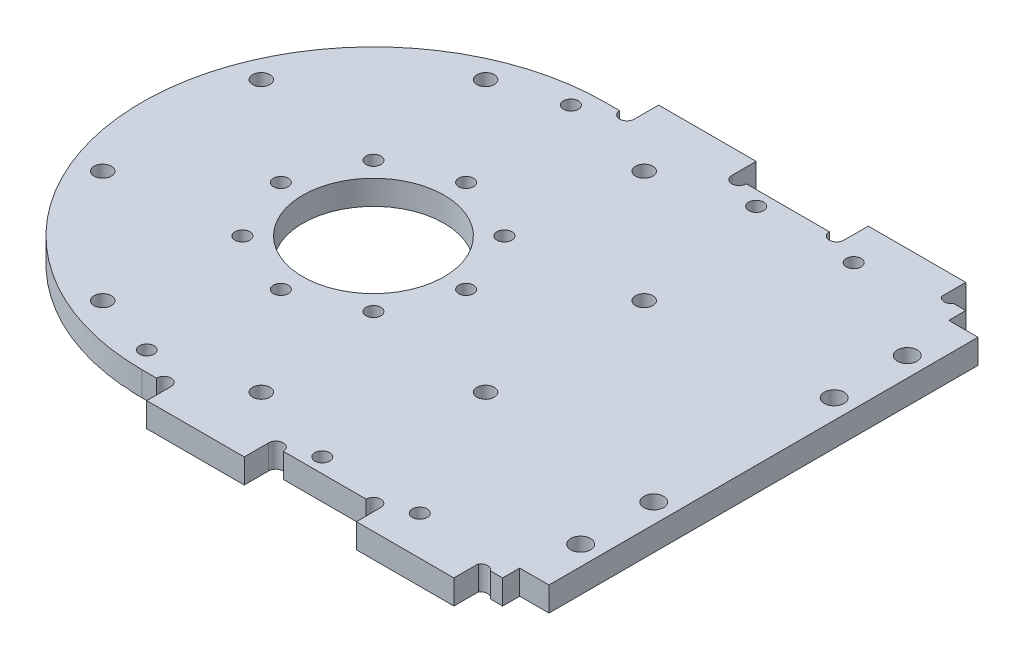
SolidWorks part; units mm, degrees
material "Thornel Mat VMA"
ref_plane "前视基准面" through (0, 0, 0) normal (0, 0, 1) x (1, 0, 0)
ref_plane "上视基准面" through (0, 0, 0) normal (0, 1, 0) x (1, 0, 0)
ref_plane "右视基准面" through (0, 0, 0) normal (1, 0, 0) x (0, 0, -1)
other "Configuration Table"
sketch "草图1" plane through (0, 0, 0) normal (0, 1, 0) x (1, 0, 0)
  line L0 (0, 47.5) -> (80, 47.5)
  line L1 (80, 47.5) -> (80, -47.5)
  line L2 (80, -47.5) -> (0, -47.5)
  arc A0 (0, 47.5) -> (0, -47.5) centre (0, 0) ccw
  dimension "D1" = 47.5
  dimension "D2" = 80
extrude "凸台-拉伸1" add sketch "草图1" along normal mid plane 5
fillet "圆角1" radius 3 2 edges at (80, 0, -47.5) (80, 0, 47.5)
sketch "草图2" plane through (0, 2.5, 0) normal (0, 1, 0) x (1, 0, 0)
  line L0 (-39.2649, 16.264) -> (0, 0) construction
  line L1 (0, 0) -> (-42.5, 0) construction
  circle A0 centre (0, 0) radius 42.5 construction
  circle A1 centre (-39.2649, 16.264) radius 1.775
  circle A2 centre (-16.264, 39.2649) radius 1.775
  circle A3 centre (16.264, 39.2649) radius 1.775
  circle A4 centre (39.2649, 16.264) radius 1.775
  circle A5 centre (39.2649, -16.264) radius 1.775
  circle A6 centre (16.264, -39.2649) radius 1.775
  circle A7 centre (-16.264, -39.2649) radius 1.775
  circle A8 centre (-39.2649, -16.264) radius 1.775
  point P22 (0, 0)
  dimension "D2" = 3.55
  dimension "D3" = 85
  dimension "D1" = 22.5
  dimension "D4" = 8
extrude "切除-拉伸1" cut sketch "草图2" against normal through all both and the other way through all
sketch "草图3" plane through (0, 2.5, 0) normal (0, 1, 0) x (1, 0, 0)
  line L0 (16, 6) -> (16, -6.5) construction
  line L1 (18, -8.5) -> (24.1402, -8.5) construction
  line L2 (24.2693, 8) -> (18, 8) construction
  line L3 (-3.5, -22.1) -> (3.5, -22.1) construction
  line L4 (5.9, -24.5) -> (5.9, -29.7951) construction
  line L5 (-5.9, -29.7951) -> (-5.9, -24.5) construction
  line L6 (-20.8746, 17.5) -> (-16.5, 17.5) construction
  line L7 (-14.5, 15.5) -> (-14.5, -15.5) construction
  line L8 (-16.5, -17.5) -> (-20.8746, -17.5) construction
  line L9 (16, 6) -> (16, -6.5)
  line L10 (18, -8.5) -> (24.1402, -8.5)
  line L11 (24.2693, 8) -> (18, 8)
  line L12 (-3.5, -22.1) -> (3.5, -22.1)
  line L13 (5.9, -24.5) -> (5.9, -29.7951)
  line L14 (-5.9, -29.7951) -> (-5.9, -24.5)
  line L15 (-20.8746, 17.5) -> (-16.5, 17.5)
  line L16 (-14.5, 15.5) -> (-14.5, -15.5)
  line L17 (-16.5, -17.5) -> (-20.8746, -17.5)
  line L18 (-20.8746, 20) -> (-16.5, 20)
  line L19 (-12, 15.5) -> (-12, -15.5)
  line L20 (-16.5, -20) -> (-20.8746, -20)
  line L21 (15, 6) -> (15, -6.5)
  line L22 (18, -9.5) -> (24.1402, -9.5)
  line L23 (24.2693, 9) -> (18, 9)
  line L24 (-3.5, -21.1) -> (3.5, -21.1)
  line L25 (6.9, -24.5) -> (6.9, -29.7951)
  line L26 (-6.9, -29.7951) -> (-6.9, -24.5)
  arc A0 (18, 8) -> (16, 6) centre (18, 6) ccw construction
  arc A1 (16, -6.5) -> (18, -8.5) centre (18, -6.5) ccw construction
  arc A2 (24.1402, -8.5) -> (26.0714, -7.02) centre (24.1402, -6.5) ccw construction
  arc A3 (26.0714, -7.02) -> (26.2109, 6.48) centre (0, 0) ccw construction
  arc A4 (26.2109, 6.48) -> (24.2693, 8) centre (24.2693, 6) ccw construction
  arc A5 (5.9, -24.5) -> (3.5, -22.1) centre (3.5, -24.5) ccw construction
  arc A6 (3.78, -32.1787) -> (5.9, -29.7951) centre (3.5, -29.7951) ccw construction
  arc A7 (-3.78, -32.1787) -> (3.78, -32.1787) centre (0, 0) ccw construction
  arc A8 (-5.9, -29.7951) -> (-3.78, -32.1787) centre (-3.5, -29.7951) ccw construction
  arc A9 (-3.5, -22.1) -> (-5.9, -24.5) centre (-3.5, -24.5) ccw construction
  arc A10 (-20.8746, 17.5) -> (-22.4804, 16.6923) centre (-20.8746, 15.5) ccw construction
  arc A11 (-14.5, 15.5) -> (-16.5, 17.5) centre (-16.5, 15.5) ccw construction
  arc A12 (-16.5, -17.5) -> (-14.5, -15.5) centre (-16.5, -15.5) ccw construction
  arc A13 (-22.4804, 16.6923) -> (-22.4804, -16.6923) centre (0, 0) ccw construction
  arc A14 (-22.4804, -16.6923) -> (-20.8746, -17.5) centre (-20.8746, -15.5) ccw construction
  arc A15 (18, 8) -> (16, 6) centre (18, 6) ccw
  arc A16 (16, -6.5) -> (18, -8.5) centre (18, -6.5) ccw
  arc A17 (24.1402, -8.5) -> (26.0714, -7.02) centre (24.1402, -6.5) ccw
  arc A18 (26.0714, -7.02) -> (26.2109, 6.48) centre (0, 0) ccw
  arc A19 (26.2109, 6.48) -> (24.2693, 8) centre (24.2693, 6) ccw
  arc A20 (5.9, -24.5) -> (3.5, -22.1) centre (3.5, -24.5) ccw
  arc A21 (3.78, -32.1787) -> (5.9, -29.7951) centre (3.5, -29.7951) ccw
  arc A22 (-3.78, -32.1787) -> (3.78, -32.1787) centre (0, 0) ccw
  arc A23 (-5.9, -29.7951) -> (-3.78, -32.1787) centre (-3.5, -29.7951) ccw
  arc A24 (-3.5, -22.1) -> (-5.9, -24.5) centre (-3.5, -24.5) ccw
  arc A25 (-20.8746, 17.5) -> (-22.4804, 16.6923) centre (-20.8746, 15.5) ccw
  arc A26 (-14.5, 15.5) -> (-16.5, 17.5) centre (-16.5, 15.5) ccw
  arc A27 (-16.5, -17.5) -> (-14.5, -15.5) centre (-16.5, -15.5) ccw
  arc A28 (-22.4804, 16.6923) -> (-22.4804, -16.6923) centre (0, 0) ccw
  arc A29 (-22.4804, -16.6923) -> (-20.8746, -17.5) centre (-20.8746, -15.5) ccw
  arc A30 (-12, 15.5) -> (-16.5, 20) centre (-16.5, 15.5) ccw
  arc A31 (-16.5, -20) -> (-12, -15.5) centre (-16.5, -15.5) ccw
  arc A32 (-24.4875, -18.1827) -> (-20.8746, -20) centre (-20.8746, -15.5) ccw
  arc A33 (-24.4875, 18.1827) -> (-24.4875, -18.1827) centre (0, 0) ccw
  arc A34 (-20.8746, 20) -> (-24.4875, 18.1827) centre (-20.8746, 15.5) ccw
  arc A35 (15, -6.5) -> (18, -9.5) centre (18, -6.5) ccw
  arc A36 (24.1402, -9.5) -> (27.037, -7.28) centre (24.1402, -6.5) ccw
  arc A37 (27.037, -7.28) -> (27.1816, 6.72) centre (0, 0) ccw
  arc A38 (27.1816, 6.72) -> (24.2693, 9) centre (24.2693, 6) ccw
  arc A39 (18, 9) -> (15, 6) centre (18, 6) ccw
  arc A40 (6.9, -24.5) -> (3.5, -21.1) centre (3.5, -24.5) ccw
  arc A41 (3.8967, -33.1719) -> (6.9, -29.7951) centre (3.5, -29.7951) ccw
  arc A42 (-3.8967, -33.1719) -> (3.8967, -33.1719) centre (0, 0) ccw
  arc A43 (-6.9, -29.7951) -> (-3.8967, -33.1719) centre (-3.5, -29.7951) ccw
  arc A44 (-3.5, -21.1) -> (-6.9, -24.5) centre (-3.5, -24.5) ccw
  dimension "D1" = 2.5
  dimension "D2" = 1
  dimension "D3" = 1
sketch "草图4" plane through (0, 2.5, 0) normal (0, 1, 0) x (1, 0, 0)
  line L0 (77, 47.5) -> (0, 47.5) construction
  line L1 (0, -47.5) -> (77, -47.5) construction
  line L2 (80, -44.5) -> (80, 44.5) construction
  circle A0 centre (76, -33.5) radius 2.025
  circle A2 centre (76, 33.5) radius 2.025
  circle A3 centre (76, 18.5) radius 2.025
  circle A4 centre (76, -18.5) radius 2.025
  circle A5 centre (76, 18.5) radius 2.025 construction
  dimension "D1" = 4.05
  dimension "D3" = 14
  dimension "D4" = 4
  dimension "D5" = 4
  dimension "D6" = 15
  dimension "D2" = 14
extrude "切除-拉伸3" cut sketch "草图4" against normal through all both
sketch "草图12" plane through (0, 2.5, 0) normal (0, 1, 0) x (1, 0, 0)
  line L0 (0, -47.5) -> (77, -47.5) construction
  line L1 (80, -44) -> (74, -44)
  line L2 (80, -44) -> (80, -47.5)
  line L3 (80, -47.5) -> (74, -47.5)
  line L4 (74, -44) -> (74, -47.5)
  line L5 (80, -44) -> (74, -47.5) construction
  line L6 (80, -47.5) -> (74, -44) construction
  line L7 (80, -44.5) -> (80, 44.5) construction
  point P0 (77, -45.75)
  dimension "D1" = 3.5
  dimension "D2" = 6
extrude "切除-拉伸9" cut sketch "草图12" against normal blind 10
sketch "草图14" plane through (0, 0, 47.5) normal (0, 0, 1) x (1, 0, 0)
  line L0 (0, 2.5) -> (74, 2.5) construction
  line L1 (49, -2.5) -> (69, -2.5)
  line L2 (49, -2.5) -> (49, 2.5)
  line L3 (49, 2.5) -> (69, 2.5)
  line L4 (69, -2.5) -> (69, 2.5)
  line L5 (49, -2.5) -> (69, 2.5) construction
  line L6 (49, 2.5) -> (69, -2.5) construction
  line L7 (26, -2.5) -> (6, -2.5)
  line L8 (26, -2.5) -> (26, 2.5)
  line L9 (26, 2.5) -> (6, 2.5)
  line L10 (6, -2.5) -> (6, 2.5)
  line L11 (26, -2.5) -> (6, 2.5) construction
  line L12 (26, 2.5) -> (6, -2.5) construction
  line L13 (74, -2.5) -> (74, 2.5) construction
  line L14 (0, -2.5) -> (74, -2.5) construction
  point P0 (59, 0)
  point P6 (16, 0)
  dimension "D1" = 6
  dimension "D2" = 20
  dimension "D3" = 20
  dimension "D4" = 5
extrude "凸台-拉伸3" add sketch "草图14" along normal blind 5
sketch "草图15" plane through (0, 2.5, 0) normal (0, 1, 0) x (1, 0, 0)
  line L0 (0, -47.5) -> (6, -47.5) construction
  line L1 (26, -47.5) -> (49, -47.5) construction
  line L2 (69, -47.5) -> (74, -47.5) construction
  line L3 (26, -47.5) -> (29, -47.5)
  line L4 (46, -47.5) -> (49, -47.5)
  line L5 (71.5, -47.5) -> (69, -47.5)
  line L6 (3, -47.5) -> (6, -47.5)
  arc A0 (6, -47.5) -> (3, -47.5) centre (4.5, -47.5) ccw
  arc A1 (26, -47.5) -> (29, -47.5) centre (27.5, -47.5) cw
  arc A2 (49, -47.5) -> (46, -47.5) centre (47.5, -47.5) ccw
  arc A3 (69, -47.5) -> (71.5, -47.5) centre (70.25, -48.3292) cw
  dimension "D1" = 1.5
extrude "切除-拉伸10" cut sketch "草图15" against normal blind 5
mirror "镜向4" about plane through (0, 0, 0) normal (0, 0, 1) of "凸台-拉伸3"
sketch "草图16" plane through (0, 2.5, 0) normal (0, 1, 0) x (1, 0, 0)
  circle A0 centre (34, -44.5) radius 1.525
  circle A1 centre (54, -44.5) radius 1.525
  dimension "D1" = 3.05
extrude "切除-拉伸11" cut sketch "草图16" against normal through all both
mirror "镜向5" about plane through (0, 0, 0) normal (0, 0, 1) of "切除-拉伸9", "切除-拉伸11", "切除-拉伸10"
sketch "草图18" plane through (0, 2.5, 0) normal (0, 1, 0) x (1, 0, 0)
  line L0 (16.264, 39.2649) -> (-16.264, 39.2649) construction
  line L1 (3, 47.5) -> (0, 47.5) construction
  circle A0 centre (-3, 43.5) radius 1.525
  point P6 (0, 39.2649)
  point P9 (1.5, 47.5)
  dimension "D1" = 4
  dimension "D2" = 3.05
  dimension "D3" = 3
extrude "切除-拉伸13" cut sketch "草图18" against normal blind 8
hole_wizard "孔1" positions "3D草图1" profile "草图19" legacy end condition through all
sketch3d "3D草图1"
  line L0 (-3, -2.5, -43.5) -> (-3, 2.5, -43.5) construction
  point P0 (-3, -2.5, -43.5)
sketch "草图19" plane through (-3, -2.5, -43.5) normal (1, 0, 0) x (0, 0, -1)
  line L0 (0, 0) -> (0, 5)
  line L1 (0, 5) -> (1.5, 5)
  line L2 (1.5, 5) -> (1.5, 2.5)
  line L3 (1.5, 2.5) -> (4, 0)
  line L4 (4, 0) -> (0, 0)
  line L5 (0, -6.4453) -> (0, 115.525) construction
  line L6 (-1.5, 2.5) -> (-4, 0) construction
  dimension "直径" = 3
  dimension "深度" = 5
  dimension "锥坑角度" = 90
  dimension "锥坑直径" = 8
mirror "镜向6" about plane through (0, 0, 0) normal (0, 0, 1) of "孔1"
sketch "草图20" plane through (0, 2.5, 0) normal (0, 1, 0) x (1, 0, 0)
  line L0 (-13.435, 13.435) -> (0, 0) construction
  line L1 (0, 0) -> (50000, 0) construction
  circle A0 centre (0, 0) radius 19 construction
  circle A1 centre (-13.435, 13.435) radius 1.525
  circle A2 centre (0, 19) radius 1.525
  circle A3 centre (13.435, 13.435) radius 1.525
  circle A4 centre (19, 0) radius 1.525
  circle A5 centre (13.435, -13.435) radius 1.525
  circle A6 centre (0, -19) radius 1.525
  circle A7 centre (-13.435, -13.435) radius 1.525
  circle A8 centre (-19, 0) radius 1.525
  point P16 (0, 0)
  dimension "D1" = 38
  dimension "D3" = 3.05
  dimension "D2" = 45
  dimension "D4" = 8
extrude "切除-拉伸14" cut sketch "草图20" against normal through all
sketch "草图21" plane through (0, -2.5, 0) normal (0, -1, 0) x (1, 0, 0)
  circle A0 centre (0, 0) radius 14.5
  dimension "D1" = 29
extrude "切除-拉伸15" cut sketch "草图21" against normal through all
